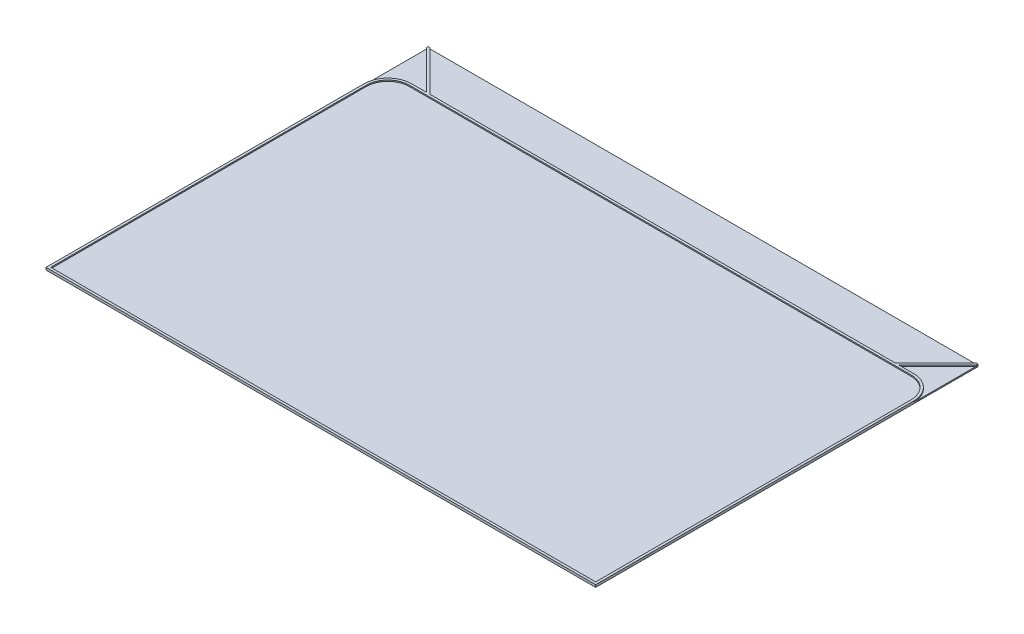
SolidWorks part; units mm, degrees
ref_plane "Front Plane" through (0, 0, 0) normal (0, 0, 1) x (1, 0, 0)
ref_plane "Top Plane" through (0, 0, 0) normal (0, 1, 0) x (1, 0, 0)
ref_plane "Right Plane" through (0, 0, 0) normal (1, 0, 0) x (0, 0, -1)
sketch "Sketch1" plane through (0, 0, 0) normal (0, 1, 0) x (1, 0, 0)
  line L1 (-115, 80) -> (115, 80)
  line L2 (-115, 80) -> (-115, -80)
  line L3 (-115, -80) -> (115, -80)
  line L4 (115, 80) -> (115, -80)
  line L5 (-115, 80) -> (115, -80) construction
  line L6 (-115, -80) -> (115, 80) construction
  point P0 (0, 0)
  dimension "D1" = 230
  dimension "D2" = 160
extrude "Boss-Extrude1" add sketch "Sketch1" along normal blind 0.5
sketch "Sketch2" plane through (0, 0.5, 0) normal (0, 1, 0) x (1, 0, 0)
  line L0 (-115, 79.2929) -> (-98.7365, 63.0294)
  line L1 (-115, 80) -> (-115, -80) construction
  line L2 (-98.7365, 63.0294) -> (-97.3223, 63.0294)
  line L3 (-97.3223, 63.0294) -> (-114.2929, 80)
  line L4 (115, 80) -> (-115, 80) construction
  line L5 (-114.2929, 80) -> (-115, 80)
  line L6 (-115, 80) -> (-115, 79.2929)
  line L7 (0, 0) -> (0, 64.2929) construction
  line L8 (114.2929, 80) -> (115, 80)
  line L9 (97.3223, 63.0294) -> (114.2929, 80)
  line L10 (98.7365, 63.0294) -> (97.3223, 63.0294)
  line L11 (115, 79.2929) -> (98.7365, 63.0294)
  line L12 (115, 80) -> (115, 79.2929)
  line L13 (115, -80) -> (115, 80) construction
  line L14 (-115, -80) -> (115, -80) construction
  line L15 (-115, -80) -> (-115, 63.0294) construction
  line L16 (-115, 63.0294) -> (115, 63.0294) construction
  line L17 (115, -80) -> (115, 63.0294) construction
  line L18 (0, 63.0294) -> (0, -80) construction
  line L19 (-115, -8.4853) -> (115, -8.4853) construction
  line L20 (-115, -80) -> (115, -80)
  line L21 (115, -80) -> (115, 53.0294)
  line L22 (105, 63.0294) -> (-105, 63.0294)
  line L23 (-115, 53.0294) -> (-115, -80)
  line L24 (105, 62.0294) -> (-105, 62.0294)
  line L25 (114, -79) -> (114, 53.0294)
  line L26 (-114, -79) -> (114, -79)
  line L27 (-114, 53.0294) -> (-114, -79)
  arc A0 (105, 63.0294) -> (115, 53.0294) centre (105, 53.0294) cw
  arc A1 (-115, 53.0294) -> (-105, 63.0294) centre (-105, 53.0294) cw
  arc A2 (-114, 53.0294) -> (-105, 62.0294) centre (-105, 53.0294) cw
  arc A3 (105, 62.0294) -> (114, 53.0294) centre (105, 53.0294) cw
  point P314 (0, -8.4853)
  line M6 (115, -80) -> (115, 80)
  line M7 (115, 80) -> (-115, 80)
  line M8 (-115, 80) -> (-115, -80)
  line M9 (-115, -80) -> (115, -80)
  dimension "D4" = 10
  dimension "D1" = 1
  dimension "D2" = 45
  dimension "D3" = 23
  dimension "D5" = 1
extrude "Boss-Extrude2" add sketch "Sketch2" along normal blind 0.5 contours A1 A0 L22 L10 L2 L24 A3 L25 L26 L27 A2 M8 M9 M6 | L2 L3 L0 M7 M8 | L11 L9 L10 M6 M7
